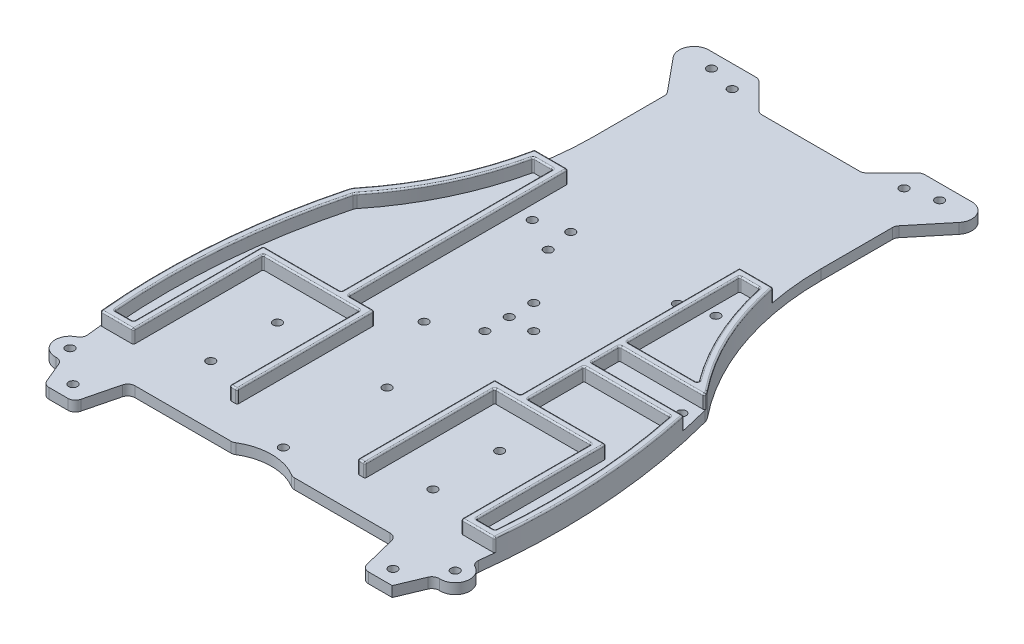
SolidWorks part; units mm, degrees
material "Delrin 2700 NC010, Low Viscosity Acetal Copolymer (SS)"
ref_plane "Front Plane" through (0, 0, 0) normal (0, 0, 1) x (1, 0, 0)
ref_plane "Top Plane" through (0, 0, 0) normal (0, 1, 0) x (1, 0, 0)
ref_plane "Right Plane" through (0, 0, 0) normal (1, 0, 0) x (0, 0, -1)
sketch "Sketch1" plane through (0, 0, 0) normal (0, 1, 0) x (1, 0, 0)
  line L0 (58.75, -109) -> (65, -94)
  line L1 (48.75, -109) -> (58.75, -109)
  line L2 (0, 91) -> (17.5, 91)
  line L3 (27.5, 101) -> (55, 101)
  line L4 (67.5, -79.4949) -> (67.5, -15.0348) construction
  line L6 (10, -94) -> (45, -94)
  line L7 (45, -94) -> (48.75, -109)
  line L8 (0, -91) -> (25.5332, -91) construction
  line L9 (0, -91) -> (0, 91)
  line L10 (17.5, 91) -> (27.5, 101)
  line L11 (55, 101) -> (38.5, 81)
  line L12 (38.5, 81) -> (38.5, 56)
  arc A0 (0, -91) -> (10, -94) centre (0, -109.1667) cw
  arc A1 (38.5, 56) -> (60, -4) centre (132.9709, 56) ccw
  circle A3 centre (65, -94) radius 5
  arc A4 (65, -94) -> (60, -4) centre (-152.3755, -60.9375) ccw
  dimension "D19" = 10
  dimension "D20" = 15
  dimension "D21" = 67.5
  dimension "D9" = 65
  dimension "D2" = 210
  dimension "D3" = 10
  dimension "D4" = 60
  dimension "D5" = 48.75
  dimension "D6" = 3
  dimension "D7" = 15
  dimension "D8" = 10
  dimension "D10" = 35
  dimension "D11" = 38.5
  dimension "D12" = 20
  dimension "D13" = 25
  dimension "D14" = 55
  dimension "D15" = 27.5
  dimension "D16" = 10
  dimension "D17" = 17.5
  dimension "D18" = 105
extrude "Boss-Extrude1" add sketch "Sketch1" along normal blind 8
hole_wizard "CSK for M2.5 Flat Head Machine Screw1" positions "Sketch5" profile "Sketch4" countersink size "M2.5" standard "ANSI Metric" end condition through all
sketch "Sketch5" plane through (0, 0, 0) normal (0, -1, 0) x (-1, 0, 0)
  line L0 (0, -91) -> (0, 91) construction
  line L1 (-48.75, -109) -> (-58.75, -109) construction
  line L2 (-27.5, 101) -> (-55, 101) construction
  point P0 (-65, -94)
  point P3 (-54, -104)
  point P5 (0, -87)
  point P10 (0, -52)
  point P12 (-37.5, -51.5)
  point P14 (-37.5, -74)
  point P16 (0, -19)
  point P18 (0, -10.75)
  point P20 (0, -2.5)
  point P22 (-24.5, 21.5)
  point P30 (-29, 93.5)
  point P32 (-38.5, 96)
  dimension "D1" = 54
  dimension "D2" = 5
  dimension "D3" = 22
  dimension "D4" = 35
  dimension "D5" = 8.25
  dimension "D6" = 8.25
  dimension "D7" = 120
  dimension "D8" = 22.5
  dimension "D9" = 35
  dimension "D10" = 37.5
  dimension "D11" = 24.5
  dimension "D12" = 24
  dimension "D13" = 5
  dimension "D14" = 7.5
  dimension "D15" = 29
  dimension "D16" = 38.5
sketch "Sketch4" plane through (65, 0, 94) normal (1, 0, 0) x (0, 0, -1)
  line L0 (0, 0) -> (0, 8)
  line L1 (0, 8) -> (1.45, 8)
  line L2 (1.45, 8) -> (1.45, 1.3)
  line L3 (1.45, 1.3) -> (2.75, 0)
  line L5 (2.75, 0) -> (0, 0)
  line L6 (-1.45, 1.3) -> (-2.75, 0) construction
  line L11 (0, -6.35) -> (0, 107.95) construction
  dimension "Thru Hole Dia." = 2.9
  dimension "Thru Hole Depth" = 8
  dimension "Near C'Sink Dia." = 5.5
  dimension "Near C'Sink Angle" = 90
mirror "Mirror1" about plane through (0, 0, 0) normal (1, 0, 0) of "CSK for M2.5 Flat Head Machine Screw1", "Boss-Extrude1"
hole_wizard "CSK for M2.5 Flat Head Machine Screw2" positions "Sketch7" profile "Sketch6" countersink size "M2.5" standard "ANSI Metric" end condition through all
sketch "Sketch7" plane through (0, 0, 0) normal (0, -1, 0) x (-1, 0, 0)
  line L0 (0, -10.75) -> (-8.25, -10.75) construction
  line L2 (14.5, 24.5) -> (-34.5, 24.5) construction
  circle A1 centre (0, -19) radius 1.45 construction
  circle A3 centre (24.5, 21.5) radius 1.45 construction
  circle A4 centre (-24.5, 21.5) radius 1.45 construction
  point P0 (-8.25, -10.75)
  point P2 (13, -26.5)
  point P4 (13.1, 15.5)
  point P6 (14.5, 24.5)
  point P8 (-34.5, 24.5)
  point P10 (-57.25, -9.75)
  dimension "D4" = 7.5
  dimension "D5" = 13
  dimension "D7" = 10
  dimension "D1" = 8.25
  dimension "D2" = 1
  dimension "D3" = 49
  dimension "D6" = 10
  dimension "D8" = 3
  dimension "D9" = 9
  dimension "D10" = 1.4
sketch "Sketch6" plane through (8.25, 0, 10.75) normal (1, 0, 0) x (0, 0, -1)
  line L0 (0, 0) -> (0, 8)
  line L1 (0, 8) -> (1.45, 8)
  line L2 (1.45, 8) -> (1.45, 1.3)
  line L3 (1.45, 1.3) -> (2.75, 0)
  line L5 (2.75, 0) -> (0, 0)
  line L6 (-1.45, 1.3) -> (-2.75, 0) construction
  line L11 (0, -6.35) -> (0, 107.95) construction
  dimension "Thru Hole Dia." = 2.9
  dimension "Thru Hole Depth" = 8
  dimension "Near C'Sink Dia." = 5.5
  dimension "Near C'Sink Angle" = 90
fillet "Fillet1" radius 2.5 17 edges at (48.75, 4, 109) (45, 4, 94) (10, 4, 94) (-45, 4, 94) (-48.75, 4, 109) (-38.5, 4, -81) (-27.5, 4, -101) (-17.5, 4, -91) (17.5, 4, -91) (27.5, 4, -101) (38.5, 4, -81) (-10, 4, 94) (63.0769, 4, 98.6154) (65.6956, 4, 89.0486) (-58.75, 4, 109) (-63.0769, 4, 98.6154) (-65.6956, 4, 89.0486)
fillet "Fillet2" radius 5 4 edges at (-55, 4, -101) (55, 4, -101) (60, 4, 4) (-60, 4, 4)
sketch "Sketch8" plane through (0, 8, 0) normal (0, 1, 0) x (1, 0, 0)
  line L0 (-40.2307, 38) -> (40.2307, 38)
  line L17 (38.5, 56) -> (38.5, 80.1019)
  line L18 (39.0716, 81.6928) -> (48.2499, 92.8181)
  line L19 (44.3931, 101) -> (28.5355, 101)
  line L20 (26.7678, 100.2678) -> (18.2322, 91.7322)
  line L21 (16.4645, 91) -> (-16.4645, 91)
  line L22 (-18.2322, 91.7322) -> (-26.7678, 100.2678)
  line L23 (-28.5355, 101) -> (-44.3931, 101)
  line L24 (-48.2499, 92.8181) -> (-39.0716, 81.6928)
  line L25 (-38.5, 80.1019) -> (-38.5, 56)
  line L26 (-62.2804, -100.5271) -> (-59.391, -107.4615)
  line L27 (-57.0833, -109) -> (-50.7019, -109)
  line L28 (-48.2766, -107.1063) -> (-45.4734, -95.8937)
  line L29 (-43.0481, -94) -> (-10.7238, -94)
  line L30 (10.7238, -94) -> (43.0481, -94)
  line L31 (45.4734, -95.8937) -> (48.2766, -107.1063)
  line L32 (50.7019, -109) -> (58.75, -109)
  line L33 (58.75, -109) -> (62.2804, -100.5271)
  line L34 (38.5, 56) -> (38.5, 80.1019)
  line L35 (39.0716, 81.6928) -> (48.2499, 92.8181)
  line L36 (44.3931, 101) -> (28.5355, 101)
  line L37 (26.7678, 100.2678) -> (18.2322, 91.7322)
  line L38 (16.4645, 91) -> (-16.4645, 91)
  line L39 (-18.2322, 91.7322) -> (-26.7678, 100.2678)
  line L40 (-28.5355, 101) -> (-44.3931, 101)
  line L41 (-48.2499, 92.8181) -> (-39.0716, 81.6928)
  line L42 (-38.5, 80.1019) -> (-38.5, 56)
  line L43 (-62.2804, -100.5271) -> (-59.391, -107.4615)
  line L44 (-57.0833, -109) -> (-50.7019, -109)
  line L45 (-48.2766, -107.1063) -> (-45.4734, -95.8937)
  line L46 (-43.0481, -94) -> (-10.7238, -94)
  line L47 (10.7238, -94) -> (43.0481, -94)
  line L48 (45.4734, -95.8937) -> (48.2766, -107.1063)
  line L49 (50.7019, -109) -> (58.75, -109)
  line L50 (58.75, -109) -> (62.2804, -100.5271)
  arc A28 (65.946, -87.0327) -> (60.2787, -5.0498) centre (-152.3755, -60.9375) ccw
  arc A29 (60.2787, -5.0498) -> (59.3399, -3.1881) centre (55.4429, -6.3207) ccw
  arc A30 (38.5, 56) -> (59.3399, -3.1881) centre (132.9709, 56) ccw
  arc A31 (39.0716, 81.6928) -> (38.5, 80.1019) centre (41, 80.1019) ccw
  arc A32 (48.2499, 92.8181) -> (44.3931, 101) centre (44.3931, 96) ccw
  arc A33 (28.5355, 101) -> (26.7678, 100.2678) centre (28.5355, 98.5) ccw
  arc A34 (16.4645, 91) -> (18.2322, 91.7322) centre (16.4645, 93.5) ccw
  arc A35 (-18.2322, 91.7322) -> (-16.4645, 91) centre (-16.4645, 93.5) ccw
  arc A36 (-26.7678, 100.2678) -> (-28.5355, 101) centre (-28.5355, 98.5) ccw
  arc A37 (-44.3931, 101) -> (-48.2499, 92.8181) centre (-44.3931, 96) ccw
  arc A38 (-38.5, 80.1019) -> (-39.0716, 81.6928) centre (-41, 80.1019) ccw
  arc A39 (-59.3399, -3.1881) -> (-38.5, 56) centre (-132.9709, 56) ccw
  arc A40 (-59.3399, -3.1881) -> (-60.2787, -5.0498) centre (-55.4429, -6.3207) ccw
  arc A41 (-60.2787, -5.0498) -> (-65.946, -87.0327) centre (152.3755, -60.9375) ccw
  arc A42 (-67.2856, -89.553) -> (-65.946, -87.0327) centre (-68.4283, -87.3294) ccw
  arc A43 (-67.2856, -89.553) -> (-64.7254, -98.9925) centre (-65, -94) ccw
  arc A44 (-62.2804, -100.5271) -> (-64.7254, -98.9925) centre (-64.5881, -101.4887) ccw
  arc A45 (-59.391, -107.4615) -> (-57.0833, -109) centre (-57.0833, -106.5) ccw
  arc A46 (-50.7019, -109) -> (-48.2766, -107.1063) centre (-50.7019, -106.5) ccw
  arc A47 (-43.0481, -94) -> (-45.4734, -95.8937) centre (-43.0481, -96.5) ccw
  arc A48 (-10.7238, -94) -> (-9.4266, -93.6371) centre (-10.7238, -91.5) ccw
  arc A49 (9.4266, -93.6371) -> (-9.4266, -93.6371) centre (0, -109.1667) ccw
  arc A50 (9.4266, -93.6371) -> (10.7238, -94) centre (10.7238, -91.5) ccw
  arc A51 (45.4734, -95.8937) -> (43.0481, -94) centre (43.0481, -96.5) ccw
  arc A52 (48.2766, -107.1063) -> (50.7019, -109) centre (50.7019, -106.5) ccw
  arc A53 (64.7254, -98.9925) -> (62.2804, -100.5271) centre (64.5881, -101.4887) ccw
  arc A54 (64.7254, -98.9925) -> (67.2856, -89.553) centre (65, -94) ccw
  arc A55 (65.946, -87.0327) -> (67.2856, -89.553) centre (68.4283, -87.3294) ccw
  arc A56 (65.946, -87.0327) -> (60.2787, -5.0498) centre (-152.3755, -60.9375) ccw
  arc A57 (60.2787, -5.0498) -> (59.3399, -3.1881) centre (55.4429, -6.3207) ccw
  arc A58 (38.5, 56) -> (59.3399, -3.1881) centre (132.9709, 56) ccw
  arc A59 (39.0716, 81.6928) -> (38.5, 80.1019) centre (41, 80.1019) ccw
  arc A60 (48.2499, 92.8181) -> (44.3931, 101) centre (44.3931, 96) ccw
  arc A61 (28.5355, 101) -> (26.7678, 100.2678) centre (28.5355, 98.5) ccw
  arc A62 (16.4645, 91) -> (18.2322, 91.7322) centre (16.4645, 93.5) ccw
  arc A63 (-18.2322, 91.7322) -> (-16.4645, 91) centre (-16.4645, 93.5) ccw
  arc A64 (-26.7678, 100.2678) -> (-28.5355, 101) centre (-28.5355, 98.5) ccw
  arc A65 (-44.3931, 101) -> (-48.2499, 92.8181) centre (-44.3931, 96) ccw
  arc A66 (-38.5, 80.1019) -> (-39.0716, 81.6928) centre (-41, 80.1019) ccw
  arc A67 (-59.3399, -3.1881) -> (-38.5, 56) centre (-132.9709, 56) ccw
  arc A68 (-59.3399, -3.1881) -> (-60.2787, -5.0498) centre (-55.4429, -6.3207) ccw
  arc A69 (-60.2787, -5.0498) -> (-65.946, -87.0327) centre (152.3755, -60.9375) ccw
  arc A70 (-67.2856, -89.553) -> (-65.946, -87.0327) centre (-68.4283, -87.3294) ccw
  arc A71 (-67.2856, -89.553) -> (-64.7254, -98.9925) centre (-65, -94) ccw
  arc A72 (-62.2804, -100.5271) -> (-64.7254, -98.9925) centre (-64.5881, -101.4887) ccw
  arc A73 (-59.391, -107.4615) -> (-57.0833, -109) centre (-57.0833, -106.5) ccw
  arc A74 (-50.7019, -109) -> (-48.2766, -107.1063) centre (-50.7019, -106.5) ccw
  arc A75 (-43.0481, -94) -> (-45.4734, -95.8937) centre (-43.0481, -96.5) ccw
  arc A76 (-10.7238, -94) -> (-9.4266, -93.6371) centre (-10.7238, -91.5) ccw
  arc A77 (9.4266, -93.6371) -> (-9.4266, -93.6371) centre (0, -109.1667) ccw
  arc A78 (9.4266, -93.6371) -> (10.7238, -94) centre (10.7238, -91.5) ccw
  arc A79 (45.4734, -95.8937) -> (43.0481, -94) centre (43.0481, -96.5) ccw
  arc A80 (48.2766, -107.1063) -> (50.7019, -109) centre (50.7019, -106.5) ccw
  arc A81 (64.7254, -98.9925) -> (62.2804, -100.5271) centre (64.5881, -101.4887) ccw
  arc A82 (64.7254, -98.9925) -> (67.2856, -89.553) centre (65, -94) ccw
  arc A83 (65.946, -87.0327) -> (67.2856, -89.553) centre (68.4283, -87.3294) ccw
  dimension "D2" = 63
  dimension "D1" = 0
extrude "Cut-Extrude1" cut sketch "Sketch8" against normal blind 4.5 contours A67 L0 A58 L34 A59 L35 A60 L36 A61 L37 A62 L38 A63 L39 A64 L40 A65 L41 A66 L42
sketch "Sketch9" plane through (0, 8, 0) normal (0, 1, 0) x (1, 0, 0)
  line L0 (30.2307, -37.25) -> (21.5828, -37.25)
  line L1 (56.5828, -81) -> (66.5828, -81)
  line L2 (56.5828, -37.25) -> (56.5828, -81)
  line L3 (21.5828, -37.25) -> (21.5828, -82.25)
  line L4 (30.2307, -37.25) -> (56.5828, -37.25)
  line L5 (30.2307, 38) -> (30.2307, -37.25)
  line L6 (-50.7019, -109) -> (-57.0833, -109) construction
  line L7 (30.2307, -3.75) -> (59.7314, -3.75)
  line L8 (30.2307, -15.75) -> (62.8066, -15.75)
  line L9 (-30.2307, 38) -> (-30.2307, -37.25)
  line L10 (-40.2307, 38) -> (40.2307, 38) construction
  line L11 (-30.2307, -37.25) -> (-56.5828, -37.25)
  line L12 (-56.5828, -37.25) -> (-56.5828, -81)
  line L13 (-56.5828, -81) -> (-66.5828, -81)
  line L14 (-30.2307, -37.25) -> (-21.5828, -37.25)
  line L15 (-21.5828, -37.25) -> (-21.5828, -82.25)
  line L16 (0, 38) -> (0, -91.5) construction
  line L17 (-40.2307, 38) -> (40.2307, 38) construction
  line L18 (38.1917, 35.5) -> (-38.1917, 35.5)
  line L19 (-59.9727, -99.5656) -> (-57.0833, -106.5)
  line L20 (-57.0833, -106.5) -> (-50.7019, -106.5)
  line L21 (-50.7019, -106.5) -> (-47.8988, -95.2873)
  line L22 (-43.0481, -91.5) -> (-10.7238, -91.5)
  line L23 (10.7238, -91.5) -> (43.0481, -91.5)
  line L24 (47.8988, -95.2873) -> (50.7019, -106.5)
  line L25 (50.7019, -106.5) -> (57.0833, -106.5)
  line L26 (57.0833, -106.5) -> (59.9727, -99.5656)
  line L27 (38.1917, 35.5) -> (-38.1917, 35.5)
  line L28 (-59.9727, -99.5656) -> (-57.0833, -106.5)
  line L29 (-57.0833, -106.5) -> (-50.7019, -106.5)
  line L30 (-50.7019, -106.5) -> (-47.8988, -95.2873)
  line L31 (-43.0481, -91.5) -> (-10.7238, -91.5)
  line L32 (10.7238, -91.5) -> (43.0481, -91.5)
  line L33 (47.8988, -95.2873) -> (50.7019, -106.5)
  line L34 (50.7019, -106.5) -> (57.0833, -106.5)
  line L35 (57.0833, -106.5) -> (59.9727, -99.5656)
  line L36 (-31.4807, 38) -> (-31.4807, -37.25)
  line L37 (-30.2307, -36) -> (-57.8328, -36)
  line L38 (-57.8328, -36) -> (-57.8328, -79.75)
  line L39 (-57.8328, -79.75) -> (-66.5828, -79.75)
  line L40 (-30.2307, -38.5) -> (-22.8328, -38.5)
  line L41 (-22.8328, -37.25) -> (-22.8328, -82.25)
  line L42 (30.2307, -36) -> (20.3328, -36)
  line L43 (20.3328, -36) -> (20.3328, -82.25)
  line L44 (30.2307, -38.5) -> (55.3328, -38.5)
  line L45 (55.3328, -38.5) -> (55.3328, -82.25)
  line L46 (55.3328, -82.25) -> (66.5828, -82.25)
  line L47 (30.2307, -5) -> (59.7314, -5)
  line L48 (28.9807, 38) -> (28.9807, -37.25)
  line L49 (30.2307, -17) -> (62.8066, -17)
  line L50 (-28.9807, 38) -> (-28.9807, -37.25)
  line L51 (-30.2307, -38.5) -> (-55.3328, -38.5)
  line L52 (-55.3328, -38.5) -> (-55.3328, -82.25)
  line L53 (-55.3328, -82.25) -> (-66.5828, -82.25)
  line L54 (-30.2307, -36) -> (-20.3328, -36)
  line L55 (-20.3328, -37.25) -> (-20.3328, -82.25)
  line L56 (30.2307, -38.5) -> (22.8328, -38.5)
  line L57 (22.8328, -38.5) -> (22.8328, -82.25)
  line L58 (30.2307, -36) -> (57.8328, -36)
  line L59 (57.8328, -36) -> (57.8328, -79.75)
  line L60 (57.8328, -79.75) -> (66.5828, -79.75)
  line L61 (30.2307, -2.5) -> (59.7314, -2.5)
  line L62 (31.4807, 38) -> (31.4807, -37.25)
  line L63 (30.2307, -14.5) -> (62.8066, -14.5)
  line L64 (59.7314, -5) -> (60.2653, -5)
  line L65 (-55.3328, -82.25) -> (55.3328, -82.25)
  line L66 (-21.5828, -37.25) -> (-21.5828, -81) construction
  line L67 (-20.3328, -36) -> (-20.3328, -37.25)
  line L74 (-20.3328, -36) -> (-20.3328, -81) construction
  line L75 (-22.8328, -38.5) -> (-22.8328, -81) construction
  circle A0 centre (57.25, -9.75) radius 1.45 construction
  arc A1 (60.2787, -5.0498) -> (59.3399, -3.1881) centre (55.4429, -6.3207) ccw construction
  arc A2 (65.946, -87.0327) -> (60.2787, -5.0498) centre (-152.3755, -60.9375) ccw construction
  arc A20 (-60.2787, -5.0498) -> (-65.946, -87.0327) centre (152.3755, -60.9375) ccw construction
  arc A40 (-57.3914, -4.7544) -> (-38.1917, 35.5) centre (-132.9709, 56) ccw
  arc A41 (-57.3914, -4.7544) -> (-57.8608, -5.6852) centre (-55.4429, -6.3207) ccw
  arc A42 (-57.8608, -5.6852) -> (-63.4637, -86.736) centre (152.3755, -60.9375) ccw
  arc A43 (-66.1428, -91.7765) -> (-63.4637, -86.736) centre (-68.4283, -87.3294) ccw
  arc A44 (-66.1428, -91.7765) -> (-64.8627, -96.4962) centre (-65, -94) ccw
  arc A45 (-59.9727, -99.5656) -> (-64.8627, -96.4962) centre (-64.5881, -101.4887) ccw
  arc A46 (-43.0481, -91.5) -> (-47.8988, -95.2873) centre (-43.0481, -96.5) ccw
  arc A47 (10.7238, -91.5) -> (-10.7238, -91.5) centre (0, -109.1667) ccw
  arc A48 (47.8988, -95.2873) -> (43.0481, -91.5) centre (43.0481, -96.5) ccw
  arc A49 (64.8627, -96.4962) -> (59.9727, -99.5656) centre (64.5881, -101.4887) ccw
  arc A50 (64.8627, -96.4962) -> (66.1428, -91.7765) centre (65, -94) ccw
  arc A51 (63.4637, -86.736) -> (66.1428, -91.7765) centre (68.4283, -87.3294) ccw
  arc A52 (63.4637, -86.736) -> (57.8608, -5.6852) centre (-152.3755, -60.9375) ccw
  arc A53 (57.8608, -5.6852) -> (57.3914, -4.7544) centre (55.4429, -6.3207) ccw
  arc A54 (38.1917, 35.5) -> (57.3914, -4.7544) centre (132.9709, 56) ccw
  arc A55 (-57.3914, -4.7544) -> (-38.1917, 35.5) centre (-132.9709, 56) ccw
  arc A56 (-57.3914, -4.7544) -> (-57.8608, -5.6852) centre (-55.4429, -6.3207) ccw
  arc A57 (-57.8608, -5.6852) -> (-63.4637, -86.736) centre (152.3755, -60.9375) ccw
  arc A58 (-66.1428, -91.7765) -> (-63.4637, -86.736) centre (-68.4283, -87.3294) ccw
  arc A59 (-66.1428, -91.7765) -> (-64.8627, -96.4962) centre (-65, -94) ccw
  arc A60 (-59.9727, -99.5656) -> (-64.8627, -96.4962) centre (-64.5881, -101.4887) ccw
  arc A61 (-43.0481, -91.5) -> (-47.8988, -95.2873) centre (-43.0481, -96.5) ccw
  arc A62 (10.7238, -91.5) -> (-10.7238, -91.5) centre (0, -109.1667) ccw
  arc A63 (47.8988, -95.2873) -> (43.0481, -91.5) centre (43.0481, -96.5) ccw
  arc A64 (64.8627, -96.4962) -> (59.9727, -99.5656) centre (64.5881, -101.4887) ccw
  arc A65 (64.8627, -96.4962) -> (66.1428, -91.7765) centre (65, -94) ccw
  arc A66 (63.4637, -86.736) -> (66.1428, -91.7765) centre (68.4283, -87.3294) ccw
  arc A67 (63.4637, -86.736) -> (57.8608, -5.6852) centre (-152.3755, -60.9375) ccw
  arc A68 (57.8608, -5.6852) -> (57.3914, -4.7544) centre (55.4429, -6.3207) ccw
  arc A69 (38.1917, 35.5) -> (57.3914, -4.7544) centre (132.9709, 56) ccw
  line M25 (40.2307, 38) -> (-40.2307, 38)
  arc M28 (-60.2787, -5.0498) -> (-65.946, -87.0327) centre (152.3755, -60.9375) ccw
  arc M29 (-65.946, -87.0327) -> (-67.2856, -89.553) centre (-68.4283, -87.3294) cw
  arc M30 (-67.2856, -89.553) -> (-64.7254, -98.9925) centre (-65, -94) ccw
  arc M31 (-64.7254, -98.9925) -> (-62.2804, -100.5271) centre (-64.5881, -101.4887) cw
  line M32 (-62.2804, -100.5271) -> (-59.391, -107.4615)
  arc M33 (-59.391, -107.4615) -> (-57.0833, -109) centre (-57.0833, -106.5) ccw
  line M34 (-57.0833, -109) -> (-50.7019, -109)
  arc M35 (-50.7019, -109) -> (-48.2766, -107.1063) centre (-50.7019, -106.5) ccw
  line M36 (-48.2766, -107.1063) -> (-45.4734, -95.8937)
  arc M37 (-45.4734, -95.8937) -> (-43.0481, -94) centre (-43.0481, -96.5) cw
  line M38 (-43.0481, -94) -> (-10.7238, -94)
  arc M39 (-10.7238, -94) -> (-9.4266, -93.6371) centre (-10.7238, -91.5) ccw
  arc M40 (-9.4266, -93.6371) -> (9.4266, -93.6371) centre (0, -109.1667) cw
  arc M41 (9.4266, -93.6371) -> (10.7238, -94) centre (10.7238, -91.5) ccw
  line M42 (10.7238, -94) -> (43.0481, -94)
  arc M43 (43.0481, -94) -> (45.4734, -95.8937) centre (43.0481, -96.5) cw
  line M44 (45.4734, -95.8937) -> (48.2766, -107.1063)
  arc M45 (48.2766, -107.1063) -> (50.7019, -109) centre (50.7019, -106.5) ccw
  line M46 (50.7019, -109) -> (58.75, -109)
  line M47 (58.75, -109) -> (62.2804, -100.5271)
  arc M48 (62.2804, -100.5271) -> (64.7254, -98.9925) centre (64.5881, -101.4887) cw
  arc M49 (64.7254, -98.9925) -> (67.2856, -89.553) centre (65, -94) ccw
  arc M50 (67.2856, -89.553) -> (65.946, -87.0327) centre (68.4283, -87.3294) cw
  arc M51 (65.946, -87.0327) -> (60.2787, -5.0498) centre (-152.3755, -60.9375) ccw
  arc M52 (60.2787, -5.0498) -> (59.3399, -3.1881) centre (55.4429, -6.3207) ccw
  circle M54 centre (8.25, -10.75) radius 1.45
  circle M55 centre (-13, -26.5) radius 1.45
  circle M56 centre (-13.1, 15.5) radius 1.45
  circle M57 centre (-14.5, 24.5) radius 1.45
  circle M58 centre (34.5, 24.5) radius 1.45
  circle M59 centre (57.25, -9.75) radius 1.45
  circle M60 centre (-54, -104) radius 1.45
  circle M61 centre (0, -52) radius 1.45
  circle M62 centre (-37.5, -74) radius 1.45
  circle M63 centre (0, -10.75) radius 1.45
  circle M64 centre (-24.5, 21.5) radius 1.45
  circle M65 centre (65, -94) radius 1.45
  circle M66 centre (54, -104) radius 1.45
  circle M67 centre (37.5, -51.5) radius 1.45
  circle M68 centre (37.5, -74) radius 1.45
  circle M69 centre (24.5, 21.5) radius 1.45
  circle M70 centre (0, -2.5) radius 1.45
  circle M71 centre (0, -19) radius 1.45
  circle M72 centre (-37.5, -51.5) radius 1.45
  circle M73 centre (0, -87) radius 1.45
  circle M74 centre (-65, -94) radius 1.45
  dimension "D8" = 6
  dimension "D2" = 10
  dimension "D3" = 10
  dimension "D4" = 35
  dimension "D5" = 45
  dimension "D6" = 28
  dimension "D7" = 6
  dimension "D1" = 2.5
  dimension "D9" = 1.25
  dimension "D10" = 1.25
  dimension "D11" = 1.25
  dimension "D12" = 1.25
  dimension "D13" = 1.25
  dimension "D14" = 1.25
extrude "Cut-Extrude3" cut sketch "Sketch9" against normal blind 4.5 contours L54 L67 L55 L65 L43 L42 L48 L27 L50 M54 M56 M64 M70 M71 M69 M63 M61 M57 M55 | L52 L65 L41 L40 L51 M72 M62 | A56 A57 L39 L38 L37 L36 L27 A55 | L57 L65 L45 L44 L56 M67 M68 | L60 A67 L49 L62 L58 L59 | A66 A67 L46 L65 L53 A57 A58 A59 A60 L28 L29 L30 A61 L31 A62 L32 A63 L33 L34 L35 A64 A65 M65 M73 M74 M66 M60 | A67 A66 A65 A64 L35 L34 L33 A63 L32 A62 L31 A61 L30 L29 L28 A60 A59 A58 A57 L53 L46 M28 M29 M30 M31 M32 M33 M34 M35 M36 M37 M38 M39 M40 M41 M42 M43 M44 M45 M46 M47 M48 M49 M50 M51 | A69 L27 L62 L61 M58 | A69 L47 L62 L63 A67 A68 M59 | L50 L27 L48 M25 | L47 A69 A68 A67 L63 L64 M59 M51 M52
fillet "Fillet3" radius 0.5 85 edges at (-59.9074, 8, 4.0695) (-47.274, 8, -16.2408) (47.274, 8, -16.2408) (-34.6057, 8, -38) (-40.2307, 5.75, -38) (40.2307, 5.75, -38) (-45.4459, 8, -14.254) (-38.1917, 5.75, -35.5) (-31.4807, 8, 0.25) (-31.4807, 5.75, -35.5) (-44.6567, 8, 36) (-31.4807, 5.75, 36) (-57.8328, 8, 57.875) (-57.8328, 5.75, 36) (-61.0086, 8, 79.75) (-57.8328, 5.75, 79.75) (-64.1844, 5.75, 79.75) (-57.6751, 8, 5.1951) (-64.212, 8, 42.4453) (-34.8362, 8, -35.5) (64.1844, 5.75, 79.75) (57.8328, 5.75, 79.75) (57.8328, 5.75, 36) (31.4807, 5.75, 36) (45.9969, 8, 17) (31.4807, 5.75, 17) (60.5132, 5.75, 17) (61.0086, 8, 79.75) (64.6289, 8, 48.2416) (31.4807, 8, 26.5) (44.6567, 8, 36) (57.8328, 8, 57.875) (44.84, 8, -15.5488) (38.1917, 5.75, -35.5) (55.6333, 5.75, 2.5) (31.4807, 5.75, 2.5) (31.4807, 5.75, -35.5) (34.8362, 8, -35.5) (31.4807, 8, -16.5) (43.557, 8, 2.5) (34.6057, 8, -38) (-66.7975, 8, 43.3754) (67.1321, 8, 48.2227) (60.8987, 8, 82.25) (55.3328, 5.75, 82.25) (66.4647, 5.75, 82.25) (-60.8987, 8, 82.25) (-66.4647, 5.75, 82.25) (-55.3328, 5.75, 82.25) (-39.0828, 8, 38.5) (-55.3328, 5.75, 38.5) (-22.8328, 8, 60.375) (-22.8328, 5.75, 38.5) (-21.5828, 8, 82.25) (-22.8328, 5.75, 82.25) (-20.3328, 5.75, 82.25) (-20.3328, 5.75, 36) (-28.9807, 5.75, 36) (-28.9807, 5.75, -38) (28.9807, 8, -1) (28.9807, 5.75, -38) (24.6567, 8, 36) (28.9807, 5.75, 36) (20.3328, 8, 59.125) (20.3328, 5.75, 36) (21.5828, 8, 82.25) (20.3328, 5.75, 82.25) (22.8328, 5.75, 82.25) (39.0828, 8, 38.5) (22.8328, 5.75, 38.5) (55.3328, 8, 60.375) (55.3328, 5.75, 38.5) (22.8328, 8, 60.375) (-28.9807, 8, -1) (-24.6567, 8, 36) (-20.3328, 8, 59.125) (-55.3328, 8, 60.375) (59.8957, 8, 4.0465) (62.5403, 5.75, 14.5) (31.4807, 5.75, 14.5) (45.873, 8, 5) (31.4807, 5.75, 5) (60.2653, 5.75, 5) (47.0105, 8, 14.5) (31.4807, 8, 9.75)
